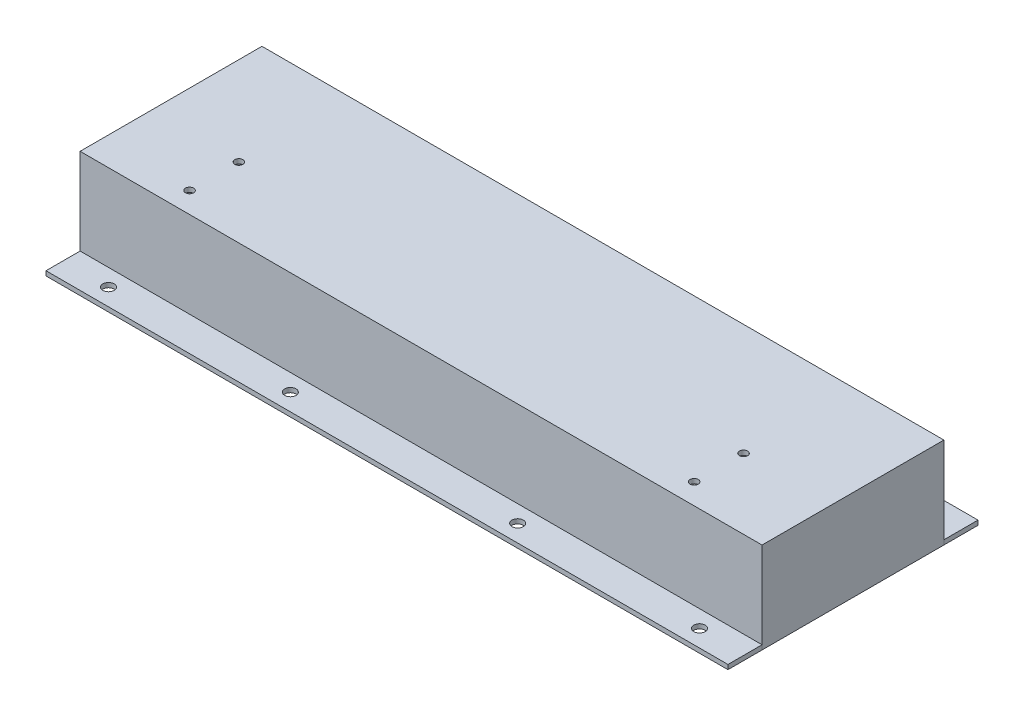
SolidWorks part; units mm, degrees
ref_plane "Plano frontal" through (0, 0, 0) normal (0, 0, 1) x (1, 0, 0)
ref_plane "Plano superior" through (0, 0, 0) normal (0, 1, 0) x (1, 0, 0)
ref_plane "Plano direito" through (0, 0, 0) normal (1, 0, 0) x (0, 0, -1)
sketch "Esboço1" plane through (0, 0, 0) normal (0, 1, 0) x (1, 0, 0)
  line L1 (150, -40) -> (-150, -40)
  line L2 (150, -40) -> (150, 40)
  line L3 (150, 40) -> (-150, 40)
  line L4 (-150, -40) -> (-150, 40)
  line L5 (150, -40) -> (-150, 40) construction
  line L6 (150, 40) -> (-150, -40) construction
  point P0 (0, 0)
  dimension "D1" = 80
  dimension "D2" = 300
extrude "Ressalto-extrusão1" add sketch "Esboço1" along normal blind 40
sketch "Esboço2" plane through (0, 0, 0) normal (0, -1, 0) x (1, 0, 0)
  line L0 (-150, -40) -> (-150, 40) construction
  line L1 (148, -38) -> (-148, -38)
  line L2 (148, -38) -> (148, 38)
  line L3 (148, 38) -> (-148, 38)
  line L4 (-148, -38) -> (-148, 38)
  line L5 (148, -38) -> (-148, 38) construction
  line L6 (148, 38) -> (-148, -38) construction
  line L7 (-150, 40) -> (150, 40) construction
  point P0 (0, 0)
  dimension "D1" = 2
  dimension "D2" = 2
extrude "Corte-extrusão1" cut sketch "Esboço2" against normal blind 38
sketch "Esboço3" plane through (0, 0, 0) normal (0, -1, 0) x (1, 0, 0)
  line L0 (-168.3788, 0) -> (176.2619, 0) construction
  line L2 (-150, 40) -> (150, 40)
  line L3 (-150, 40) -> (-150, 55)
  line L4 (-150, 55) -> (150, 55)
  line L5 (150, 40) -> (150, 55)
  line L6 (150, 40) -> (150, -40) construction
  line L7 (-150, -55) -> (150, -55)
  line L8 (150, -40) -> (150, -55)
  line L9 (-150, -40) -> (150, -40)
  line L10 (-150, -40) -> (-150, -55)
  dimension "D1" = 15
extrude "Ressalto-extrusão2" add sketch "Esboço3" against normal blind 2 separate body
sketch "Esboço4" plane through (0, 2, 0) normal (0, 1, 0) x (1, 0, 0)
  line L0 (-161.4449, -47.5) -> (159.3705, -47.5) construction
  line L1 (0, 62.2376) -> (0, -70.5342) construction
  line L3 (-183.2674, 0) -> (182.9241, 0) construction
  line L6 (150, -55) -> (-150, -55) construction
  circle A0 centre (-130, -47.5) radius 2.5
  circle A1 centre (-50, -47.5) radius 2.5
  circle A2 centre (50, -47.5) radius 2.5
  circle A3 centre (130, -47.5) radius 2.5
  circle A4 centre (130, 47.5) radius 2.5
  circle A5 centre (50, 47.5) radius 2.5
  circle A6 centre (-50, 47.5) radius 2.5
  circle A7 centre (-130, 47.5) radius 2.5
  dimension "D1" = 5
  dimension "D3" = 80
  dimension "D4" = 7.5
  dimension "D2" = 50
extrude "Corte-extrusão2" cut sketch "Esboço4" against normal through all
sketch "Esboço5" plane through (0, 40, 0) normal (0, 1, 0) x (1, 0, 0)
  line L0 (-181.4646, -20) -> (184.4723, -20) construction
  line L1 (0, -82.9624) -> (0, 72.4355) construction
  line L3 (-150, -40) -> (150, -40) construction
  circle A0 centre (-111, -9.15) radius 1.8
  circle A1 centre (111, -9.15) radius 1.8
  circle A2 centre (111, -30.85) radius 1.8
  circle A3 centre (-111, -30.85) radius 1.8
  dimension "D1" = 3.6
  dimension "D2" = 111
  dimension "D3" = 10.85
  dimension "D4" = 20
extrude "Corte-extrusão3" cut sketch "Esboço5" against normal blind 2
sketch "Esboço6" plane through (0, 0, -40) normal (0, 0, -1) x (-1, 0, 0)
  line L0 (155.8683, 20) -> (-161.1208, 20) construction
  line L1 (150, 40) -> (150, 0) construction
  line L2 (89.25, 8.75) -> (60.75, 8.75)
  line L3 (89.25, 8.75) -> (89.25, 31.25)
  line L4 (89.25, 31.25) -> (60.75, 31.25)
  line L5 (60.75, 8.75) -> (60.75, 31.25)
  line L6 (89.25, 8.75) -> (60.75, 31.25) construction
  line L7 (89.25, 31.25) -> (60.75, 8.75) construction
  point P2 (75, 20)
  dimension "D1" = 22.5
  dimension "D2" = 28.5
  dimension "D3" = 75
extrude "Corte-extrusão4" cut sketch "Esboço6" against normal blind 2
